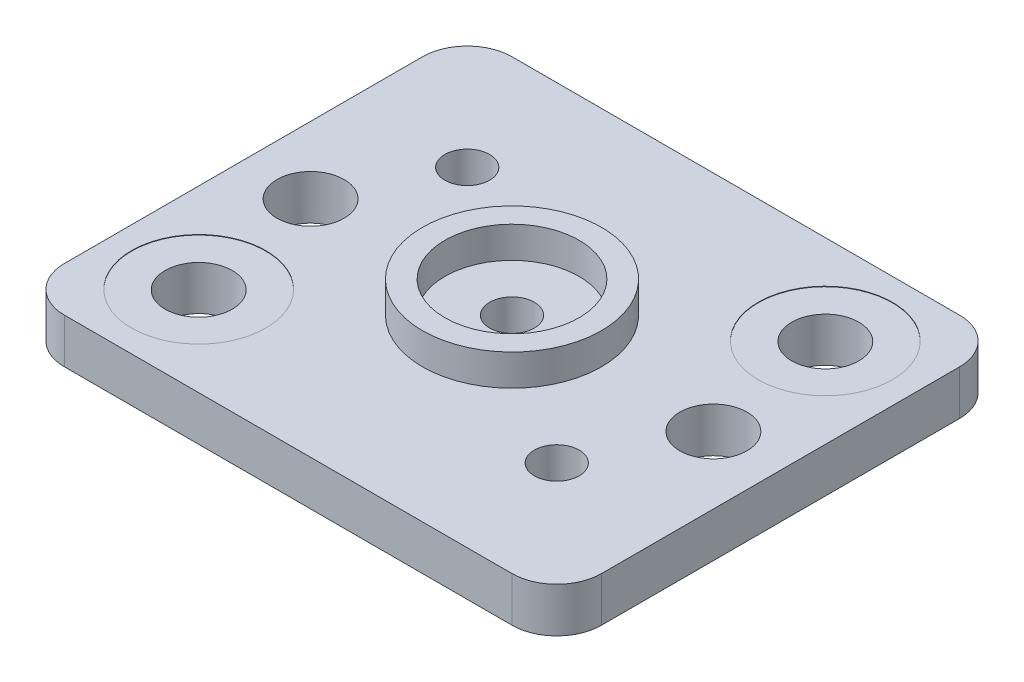
SolidWorks part; units mm, degrees
ref_plane "Alzado" through (0, 0, 0) normal (0, 0, 1) x (1, 0, 0)
ref_plane "Planta" through (0, 0, 0) normal (0, 1, 0) x (1, 0, 0)
ref_plane "Vista lateral" through (0, 0, 0) normal (1, 0, 0) x (0, 0, -1)
sketch "Croquis1" plane through (0, 0, 0) normal (0, 1, 0) x (1, 0, 0)
  line L0 (0, 0) -> (0, 6.7969) construction
  line L1 (-6, 5) -> (6, 5)
  line L2 (-6, 5) -> (-6, -5)
  line L4 (6, 5) -> (6, 0.5)
  line L7 (0, 0) -> (6.6455, 0) construction
  line L8 (-6, -5) -> (1.5, -5)
  line L9 (1.5, -5) -> (6, -5)
  line L10 (6, -5) -> (6, 0.5)
extrude "Saliente-Extruir1" add sketch "Croquis1" along normal blind 1
sketch "Croquis2" plane through (0, 1, 0) normal (0, 1, 0) x (1, 0, 0)
  circle A0 centre (4, 3) radius 1.5
  circle A1 centre (-4, -3) radius 1.5
fillet "Redondeo1" radius 1 4 edges at (6, 0.5, -5) (-6, 0.5, -5) (-6, 0.5, 5) (6, 0.5, 5)
extrude "Cortar-Extruir3" cut sketch "Croquis2" against normal blind 0.01
sketch "Croquis5" plane through (0, 0.99, 0) normal (0, 1, 0) x (1, 0, 0)
  circle A0 centre (4, 3) radius 0.75
  circle A1 centre (-4, -3) radius 0.75
  dimension "D1" = 1.5
  dimension "D2" = 1.5
extrude "Cortar-Extruir5" cut sketch "Croquis5" against normal blind 1.1
sketch "Croquis6" plane through (0, 1, 0) normal (0, 1, 0) x (1, 0, 0)
  line L0 (0, 0) -> (0, 4.211) construction
  line L1 (6, -4) -> (6, 4) construction
  line L2 (-5, -5) -> (5, -5) construction
  line L3 (0, 0) -> (-3.2392, 0) construction
  line L4 (5, 5) -> (-5, 5) construction
  line L5 (-6, 4) -> (-6, -4) construction
  circle A0 centre (4.5, 0) radius 0.75
  circle A1 centre (-4.5, 0) radius 0.75
  circle A2 centre (3.36, -2.36) radius 0.5
  circle A4 centre (-3.36, 2.36) radius 0.5
  dimension "D1" = 1.5
  dimension "D3" = 1
  dimension "D2" = 4.5
  dimension "D4" = 2.64
  dimension "D5" = 2.64
  dimension "D6" = 2.64
  dimension "D7" = 2.64
extrude "Cortar-Extruir6" cut sketch "Croquis6" against normal blind 1.1
sketch "Croquis7" plane through (0, 1, 0) normal (0, 1, 0) x (1, 0, 0)
  circle A0 centre (0, 0) radius 2
  dimension "D1" = 4
extrude "Saliente-Extruir2" add sketch "Croquis7" along normal blind 0.7
sketch "Croquis8" plane through (0, 1.7, 0) normal (0, 1, 0) x (1, 0, 0)
  circle A0 centre (0, 0) radius 1.5
  dimension "D1" = 3
extrude "Cortar-Extruir7" cut sketch "Croquis8" against normal blind 0.7
sketch "Croquis9" plane through (0, 1, 0) normal (0, 1, 0) x (1, 0, 0)
  circle A0 centre (0, 0) radius 0.5
  dimension "D1" = 1
extrude "Cortar-Extruir9" cut sketch "Croquis9" against normal blind 8
